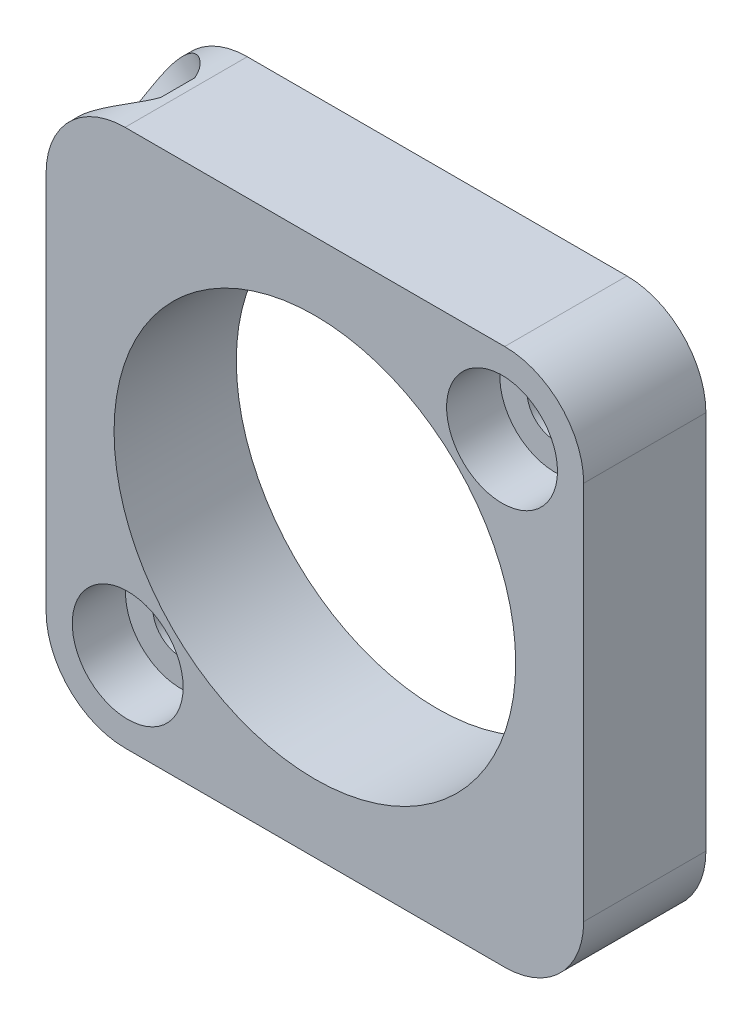
SolidWorks part; units mm, degrees
material "6061-T6 (SS)"
ref_plane "Front Plane" through (0, 0, 0) normal (0, 0, 1) x (1, 0, 0)
ref_plane "Top Plane" through (0, 0, 0) normal (0, 1, 0) x (1, 0, 0)
ref_plane "Right Plane" through (0, 0, 0) normal (1, 0, 0) x (0, 0, -1)
sketch "Sketch1" plane through (0, 0, 0) normal (1, 0, 0) x (0, 0, -1)
  line L0 (0, 0) -> (0, -33.7571) construction
  line L1 (0, 0) -> (28.0663, 0) construction
  line L2 (0, 15) -> (-3.5, 15)
  line L3 (-3.5, 15) -> (-3.5, 5.75)
  line L6 (-3.5, 5.75) -> (0, 5.75)
  line L7 (0, 5.75) -> (0, 15)
  dimension "D1" = 30
  dimension "D2" = 11.5
  dimension "D3" = 3.5
revolve "Revolve1" add sketch "Sketch1" angle 360 about L1
sketch "Sketch2" plane through (0, 0, 0) normal (0, 0, -1) x (-1, 0, 0)
  line L0 (5.3594, -5.3594) -> (-5.3594, 5.3594) construction
  line L1 (0, 0) -> (0, 3.828) construction
  point P5 (0, 0)
  dimension "D1" = 15.1587
  dimension "D2" = 45
hole_wizard "CBORE for #0 Socket Head Cap Screw1" positions "Sketch4" profile "Sketch3" counterbore size "#0" standard "Ansi Inch" end condition through all
sketch "Sketch4" plane through (-5.1442, 9.1531, 3.5) normal (0, 0, -1) x (-1, 0, 0)
  point P0 (-10.5036, -3.7937)
  point P1 (0.2152, -14.5125)
sketch "Sketch3" plane through (5.3594, 5.3594, 3.5) normal (1, 0, 0) x (0, -1, 0)
  line L0 (0, 0) -> (0, 3.5)
  line L1 (0.8064, 2.865) -> (1.4414, 3.5)
  line L2 (0.8064, 2.865) -> (0.8064, 1.524)
  line L3 (0.8064, 1.524) -> (1.5875, 1.524)
  line L4 (1.5875, 1.524) -> (1.5875, 0)
  line L5 (1.5875, 0) -> (0, 0)
  line L11 (0, -6.35) -> (0, 107.95) construction
  line L12 (1.4414, 3.5) -> (0, 3.5)
  line L13 (-0.8065, 2.865) -> (-1.4415, 3.5) construction
  dimension "Thru Hole Dia." = 1.6129
  dimension "Thru Hole Depth" = 3.5
  dimension "C'Bore Dia." = 3.175
  dimension "C'Bore Depth" = 1.524
  dimension "Far C'Sink Dia." = 2.8829
  dimension "Far C'Sink Angle" = 90
sketch "Sketch5" plane through (0, 0, 3.5) normal (0, 0, 1) x (1, 0, 0)
  line L0 (-7.6962, 7.6962) -> (7.6962, -7.6962) construction
  line L1 (-7.6962, 7.6962) -> (7.6962, 7.6962)
  line L2 (-7.6962, 7.6962) -> (-7.6962, -7.6962)
  line L3 (-7.6962, -7.6962) -> (7.6962, -7.6962)
  line L4 (7.6962, 7.6962) -> (7.6962, -7.6962)
  point P4 (0, 0)
  dimension "D1" = 15.3924
extrude "Cut-Extrude1" cut sketch "Sketch5" against normal blind 10 flip side to cut
fillet "Fillet1" radius 2.2606 4 edges at (7.6962, -7.6962, 1.75) (-7.6962, -7.6962, 1.75) (-7.6962, 7.6962, 1.75) (7.6962, 7.6962, 1.75)
sketch "Sketch6" plane through (0, 0, 0) normal (0, 1, 0) x (1, 0, 0)
  line L0 (0, 0) -> (0, -3.5) construction
  line L2 (-5.75, -3.5) -> (5.75, -3.5) construction
  point P5 (0, -1.75)
ref_plane "Plane1" through (0, 0, 1.75) normal (0, 0, 1) x (1, 0, 0)
sketch "Sketch7" plane through (0, 0, 1.75) normal (0, 0, 1) x (1, 0, 0)
  line L0 (0, 0) -> (-7.0341, 7.0341) construction
  arc A0 (-5.4356, 7.6962) -> (-7.6962, 5.4356) centre (-5.4356, 5.4356) ccw construction
  point P6 (-7.0341, 7.0341)
ref_plane "Plane2" through (-7.0341, 7.0341, 1.75) normal (-0.7071, 0.7071, 0) x (0, 0, 1)
sketch "Sketch8" plane through (-7.0341, 7.0341, 1.75) normal (-0.7071, 0.7071, 0) x (0, 0, 1)
  circle A0 centre (0, 0) radius 1.5
  dimension "D1" = 3
extrude "Cut-Extrude2" cut sketch "Sketch8" against normal blind 0.5
hole_wizard "#2-56 Tapped Hole1" positions "Sketch10" profile "Sketch9" tap size "#2-56" standard "Ansi Inch"
sketch "Sketch10" plane through (-6.6805, 6.6805, 0) normal (-0.7071, 0.7071, 0) x (-0.7071, -0.7071, 0)
  point P0 (0, 1.75)
cosmetic thread "Hole Thread1" parameters "D2"=2.1844
sketch "Sketch9" plane through (-6.6805, 6.6805, 1.75) normal (0, 0, 1) x (-0.7071, -0.7071, 0)
  line L0 (0, 0) -> (0, 3.6977)
  line L1 (0, 3.6977) -> (0.889, 3.6977)
  line L2 (0.889, 3.6977) -> (0.889, 0)
  line L5 (0.889, 0) -> (0, 0)
  line L11 (0, -6.35) -> (0, 107.95) construction
  dimension "Thru Tap Drill Dia." = 1.778
  dimension "Thru Tap Drill Depth" = 3.6977
